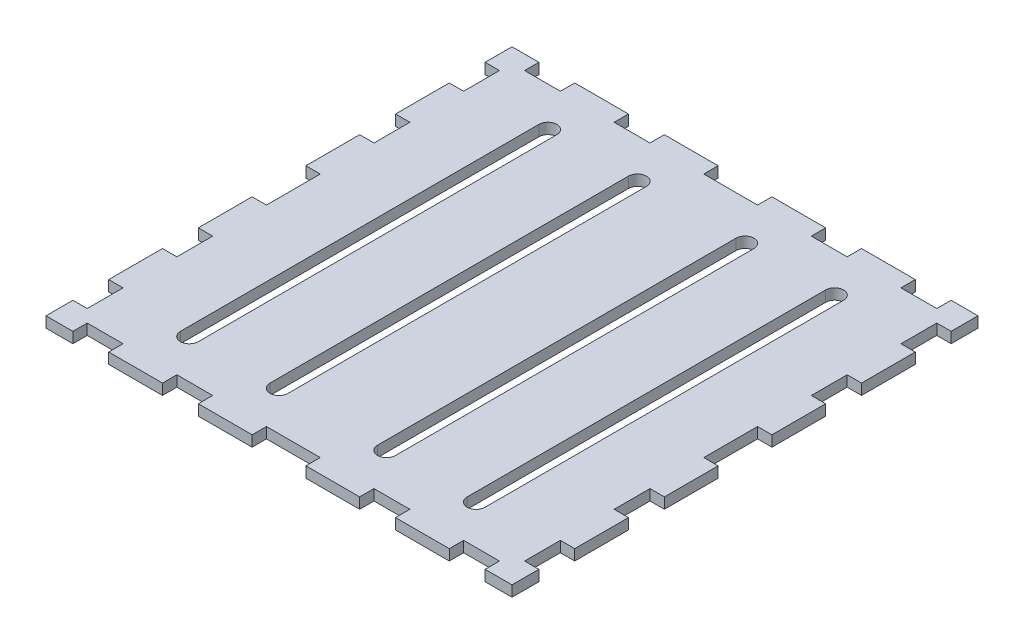
SolidWorks part; units mm, degrees
ref_plane "Front Plane" through (0, 0, 0) normal (0, 0, 1) x (1, 0, 0)
ref_plane "Top Plane" through (0, 0, 0) normal (0, 1, 0) x (1, 0, 0)
ref_plane "Right Plane" through (0, 0, 0) normal (1, 0, 0) x (0, 0, -1)
sketch "Sketch1" plane through (0, 0, 0) normal (0, 1, 0) x (1, 0, 0)
  line L0 (0, 80.1692) -> (0, -87.0923) construction
  line L3 (-65, -65) -> (-57.5, -65)
  line L5 (-65, 47.5) -> (-65, 32.5)
  line L6 (7.5, -65) -> (7.5, -61)
  line L8 (-7.5, 65) -> (-7.5, 61)
  line L9 (-7.5, 61) -> (7.5, 61)
  line L10 (7.5, 65) -> (7.5, 61)
  line L11 (-7.5, -61) -> (7.5, -61)
  line L12 (-7.5, -65) -> (-7.5, -61)
  line L13 (7.5, 65) -> (22.5, 65)
  line L14 (7.5, -65) -> (22.5, -65)
  line L15 (-40, 78.4584) -> (-40, -95.43) construction
  line L16 (-32.5, 61) -> (-22.5, 61)
  line L17 (-22.5, 61) -> (-22.5, 65)
  line L18 (-32.5, 61) -> (-32.5, 65)
  line L19 (-57.5, 65) -> (-57.5, 61)
  line L20 (-57.5, 61) -> (-47.5, 61)
  line L21 (-47.5, 61) -> (-47.5, 65)
  line L22 (-47.5, 65) -> (-32.5, 65)
  line L23 (-22.5, 65) -> (-7.5, 65)
  line L24 (57.5, 65) -> (57.5, 61)
  line L25 (57.5, 61) -> (47.5, 61)
  line L26 (47.5, 61) -> (47.5, 65)
  line L27 (32.5, 61) -> (32.5, 65)
  line L28 (32.5, 61) -> (22.5, 61)
  line L29 (22.5, 61) -> (22.5, 65)
  line L30 (57.5, -65) -> (57.5, -61)
  line L31 (57.5, -61) -> (47.5, -61)
  line L32 (47.5, -61) -> (47.5, -65)
  line L33 (32.5, -61) -> (22.5, -61)
  line L34 (22.5, -61) -> (22.5, -65)
  line L35 (-22.5, -61) -> (-22.5, -65)
  line L36 (-32.5, -61) -> (-22.5, -61)
  line L37 (-32.5, -61) -> (-32.5, -65)
  line L38 (-57.5, -65) -> (-57.5, -61)
  line L39 (-47.5, -61) -> (-47.5, -65)
  line L40 (-57.5, -61) -> (-47.5, -61)
  line L41 (-22.5, -65) -> (-7.5, -65)
  line L42 (-47.5, -65) -> (-32.5, -65)
  line L43 (57.5, -65) -> (65, -65)
  line L44 (32.5, -61) -> (32.5, -65)
  line L45 (32.5, -65) -> (47.5, -65)
  line L46 (57.5, 65) -> (65, 65)
  line L47 (32.5, 65) -> (47.5, 65)
  line L48 (65, -7.5) -> (61, -7.5)
  line L49 (61, -7.5) -> (61, 7.5)
  line L50 (61, 7.5) -> (65, 7.5)
  line L51 (65, 22.5) -> (61, 22.5)
  line L52 (61, 22.5) -> (61, 32.5)
  line L53 (61, 32.5) -> (65, 32.5)
  line L54 (65, 47.5) -> (61, 47.5)
  line L55 (61, 47.5) -> (61, 57.5)
  line L56 (61, 57.5) -> (65, 57.5)
  line L57 (65, 47.5) -> (65, 32.5)
  line L58 (65, 22.5) -> (65, 7.5)
  line L60 (61, -57.5) -> (65, -57.5)
  line L61 (61, -47.5) -> (61, -57.5)
  line L62 (65, -47.5) -> (61, -47.5)
  line L63 (61, -22.5) -> (61, -32.5)
  line L64 (61, -32.5) -> (65, -32.5)
  line L65 (65, -22.5) -> (61, -22.5)
  line L68 (-61, -57.5) -> (-65, -57.5)
  line L69 (-61, -47.5) -> (-61, -57.5)
  line L70 (-65, -47.5) -> (-61, -47.5)
  line L71 (-61, -32.5) -> (-65, -32.5)
  line L72 (-61, -22.5) -> (-61, -32.5)
  line L73 (-65, -22.5) -> (-61, -22.5)
  line L74 (-65, -7.5) -> (-61, -7.5)
  line L75 (-61, -7.5) -> (-61, 7.5)
  line L76 (-61, 7.5) -> (-65, 7.5)
  line L77 (-61, 22.5) -> (-61, 32.5)
  line L78 (-65, 22.5) -> (-61, 22.5)
  line L79 (-61, 32.5) -> (-65, 32.5)
  line L80 (-65, 47.5) -> (-61, 47.5)
  line L81 (-61, 47.5) -> (-61, 57.5)
  line L82 (-61, 57.5) -> (-65, 57.5)
  line L84 (65, -7.5) -> (65, -22.5)
  line L85 (65, -32.5) -> (65, -47.5)
  line L86 (65, -57.5) -> (65, -65)
  line L87 (-14.7774, 72.9742) -> (-14.7774, -82.3113) construction
  line L89 (-65, -7.5) -> (-65, -22.5)
  line L91 (-65, 65) -> (-57.5, 65)
  line L94 (-65, 22.5) -> (-65, 7.5)
  line L95 (-65, -57.5) -> (-65, -65)
  line L96 (-65, -32.5) -> (-65, -47.5)
  line L97 (-40, 50) -> (-40, -50) construction
  line L98 (-65, 57.5) -> (-65, 65)
  line L99 (65, 65) -> (65, 57.5)
  line L100 (-37.5, 50) -> (-37.5, -50)
  line L101 (-42.5, 50) -> (-42.5, -50)
  line L102 (-15, 50) -> (-15, -50) construction
  line L103 (-12.5, 50) -> (-12.5, -50)
  line L104 (-17.5, 50) -> (-17.5, -50)
  line L105 (40, 50) -> (40, -50) construction
  line L106 (37.5, 50) -> (37.5, -50)
  line L107 (42.5, 50) -> (42.5, -50)
  line L108 (15, 50) -> (15, -50) construction
  line L109 (12.5, 50) -> (12.5, -50)
  line L110 (17.5, 50) -> (17.5, -50)
  arc A0 (-37.5, 50) -> (-42.5, 50) centre (-40, 50) ccw
  arc A1 (-42.5, -50) -> (-37.5, -50) centre (-40, -50) ccw
  arc A2 (-12.5, 50) -> (-17.5, 50) centre (-15, 50) ccw
  arc A3 (-17.5, -50) -> (-12.5, -50) centre (-15, -50) ccw
  arc A4 (37.5, 50) -> (42.5, 50) centre (40, 50) cw
  arc A5 (42.5, -50) -> (37.5, -50) centre (40, -50) cw
  arc A6 (12.5, 50) -> (17.5, 50) centre (15, 50) cw
  arc A7 (17.5, -50) -> (12.5, -50) centre (15, -50) cw
  point P91 (-40, -65)
  point P94 (-40, 0)
  point P99 (-37.5, 0)
  point P100 (-40, 65)
  point P105 (-15, 0)
  point P110 (40, 0)
  point P117 (15, 0)
  dimension "D3" = 15
  dimension "D4" = 10
  dimension "D5" = 15
  dimension "D6" = 7.5
  dimension "D7" = 4
  dimension "D8" = 15
  dimension "D9" = 10
  dimension "D10" = 15
  dimension "D11" = 10
  dimension "D12" = 10
  dimension "D13" = 10
  dimension "D14" = 15
  dimension "D15" = 10
  dimension "D16" = 4
  dimension "D17" = 15
  dimension "D18" = 15
  dimension "D19" = 4
  dimension "D20" = 15
  dimension "D21" = 10
  dimension "D22" = 10
  dimension "D23" = 4
  dimension "D24" = 4
  dimension "D25" = 15
  dimension "D26" = 15
  dimension "D27" = 15
  dimension "D28" = 15
  dimension "D29" = 10
  dimension "D30" = 10
  dimension "D31" = 100
  dimension "D32" = 5
  dimension "D33" = 2
extrude "Boss-Extrude1" add sketch "Sketch1" along normal blind 3
